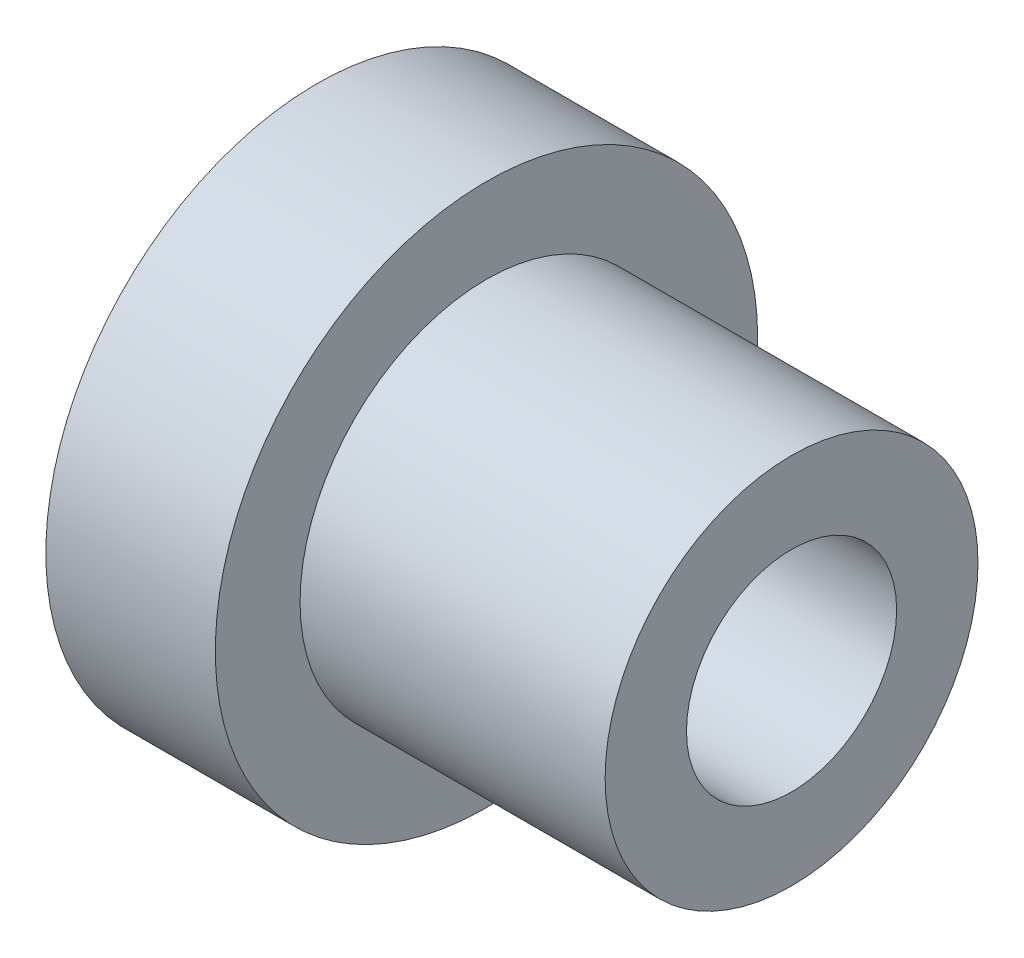
SolidWorks part; units mm, degrees
ref_plane "Front Plane" through (0, 0, 0) normal (0, 0, 1) x (1, 0, 0)
ref_plane "Top Plane" through (0, 0, 0) normal (0, 1, 0) x (1, 0, 0)
ref_plane "Right Plane" through (0, 0, 0) normal (1, 0, 0) x (0, 0, -1)
sketch "Sketch1" plane through (0, 0, 0) normal (0, 0, 1) x (1, 0, 0)
  line L0 (-2.85, 5.5) -> (-2.85, 8)
  line L1 (-2.85, 8) -> (-7.85, 8)
  line L2 (-7.85, 8) -> (-7.85, 6)
  line L3 (-7.85, 6) -> (-5.35, 6)
  line L4 (-5.35, 6) -> (-5.35, 3.1)
  line L5 (-5.35, 3.1) -> (6.15, 3.1)
  line L6 (6.15, 3.1) -> (6.15, 5.5)
  line L7 (6.15, 5.5) -> (-2.85, 5.5)
  line L8 (-7.85, 0) -> (6.15, 0) construction
revolve "Revolve1" add sketch "Sketch1" angle 360 about L8
